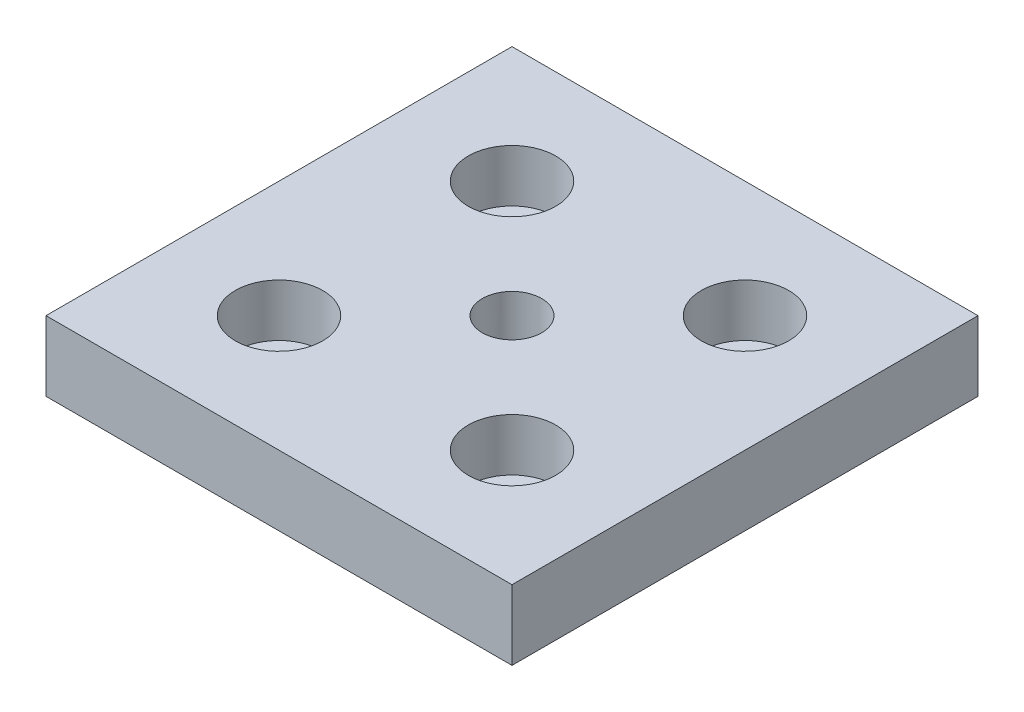
SolidWorks part; units mm, degrees
material "Алюминиевый сплав"
ref_plane "Спереди" through (0, 0, 0) normal (0, 0, 1) x (1, 0, 0)
ref_plane "Сверху" through (0, 0, 0) normal (0, 1, 0) x (1, 0, 0)
ref_plane "Справа" through (0, 0, 0) normal (1, 0, 0) x (0, 0, -1)
sketch "Эскиз1" plane through (0, 0, 0) normal (0, 1, 0) x (1, 0, 0)
  line L1 (-40, -40) -> (40, -40)
  line L2 (-40, -40) -> (-40, 40)
  line L3 (-40, 40) -> (40, 40)
  line L4 (40, -40) -> (40, 40)
  line L5 (-40, -40) -> (40, 40) construction
  line L6 (-40, 40) -> (40, -40) construction
  point P0 (0, 0)
  dimension "D1" = 80
extrude "Бобышка-Вытянуть1" add sketch "Эскиз1" along normal blind 12
hole_wizard "Отверстие обработанное метчиком M121" positions "Эскиз8" profile "Эскиз9" tap size "M12" standard "ISO" end condition up to next
sketch "Эскиз8" plane through (0, 12, 0) normal (0, 1, 0) x (1, 0, 0)
  point P0 (0, 0)
sketch "Эскиз9" plane through (0, 12, 0) normal (1, 0, 0) x (0, 0, 1)
  line L0 (0, 0) -> (0, 12)
  line L1 (0, 12) -> (5.1, 12)
  line L2 (5.1, 12) -> (5.1, 0)
  line L5 (5.1, 0) -> (0, 0)
  line L11 (0, -6.35) -> (0, 107.95) construction
  dimension "Диаметр проходного сверла" = 10.2
  dimension "Глубина проходного сверла" = 12
cosmetic thread "Отверстие резьбы3" parameters "D2"=12
sketch "Эскиз12" plane through (0, 12, 0) normal (0, 1, 0) x (1, 0, 0)
  line L1 (20, -20) -> (-20, -20) construction
  line L2 (20, -20) -> (20, 20) construction
  line L3 (20, 20) -> (-20, 20) construction
  line L4 (-20, -20) -> (-20, 20) construction
  line L5 (20, -20) -> (-20, 20) construction
  line L6 (20, 20) -> (-20, -20) construction
  circle A0 centre (-20, 20) radius 4.5
  circle A1 centre (20, 20) radius 4.5
  circle A2 centre (20, -20) radius 4.5
  circle A3 centre (-20, -20) radius 4.5
  point P0 (0, 0)
  dimension "D2" = 9
  dimension "D1" = 40
extrude "Вырез-Вытянуть1" cut sketch "Эскиз12" against normal through all
sketch "Эскиз13" plane through (0, 12, 0) normal (0, 1, 0) x (1, 0, 0)
  circle A0 centre (-20, 20) radius 7.5
  circle A1 centre (20, 20) radius 7.5
  circle A2 centre (20, -20) radius 7.5
  circle A3 centre (-20, -20) radius 7.5
  dimension "D1" = 15
extrude "Вырез-Вытянуть2" cut sketch "Эскиз13" against normal blind 9
